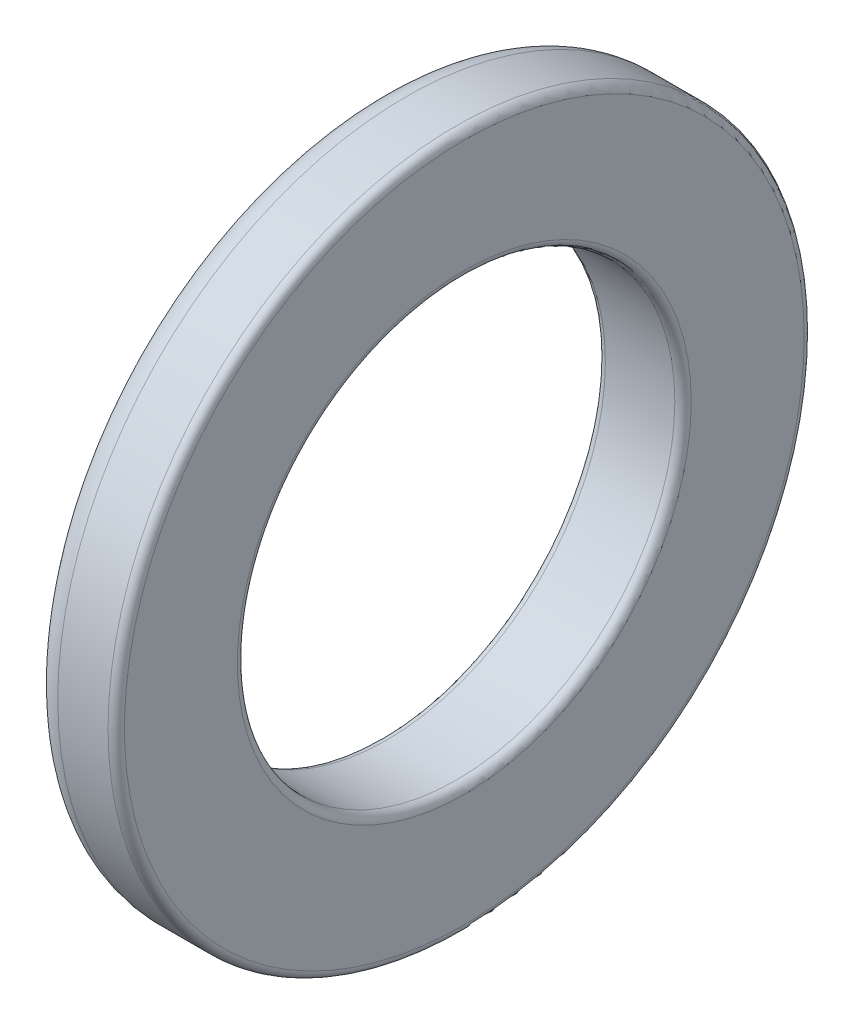
SolidWorks part; units mm, degrees
material "Chrome Stainless Steel"
ref_plane "Front Plane" through (0, 0, 0) normal (0, 0, 1) x (1, 0, 0)
ref_plane "Top Plane" through (0, 0, 0) normal (0, 1, 0) x (1, 0, 0)
ref_plane "Right Plane" through (0, 0, 0) normal (1, 0, 0) x (0, 0, -1)
sketch "Sketch1" plane through (0, 0, 0) normal (1, 0, 0) x (0, 0, -1)
  circle A0 centre (0, 0) radius 4
  circle A1 centre (0, 0) radius 6.365
  dimension "D1" = 12.73
  dimension "D2" = 8
extrude "Boss-Extrude1" add sketch "Sketch1" along normal blind 1.57
fillet "Fillet1" radius 0.15 2 edges at (1.57, 0, -4) (1.57, 0, -6.365)
fillet "Fillet2" radius 0.15 1 edges at (0, 0, -4)
fillet "Fillet3" radius 0.5 1 edges at (0, 0, -6.365)
